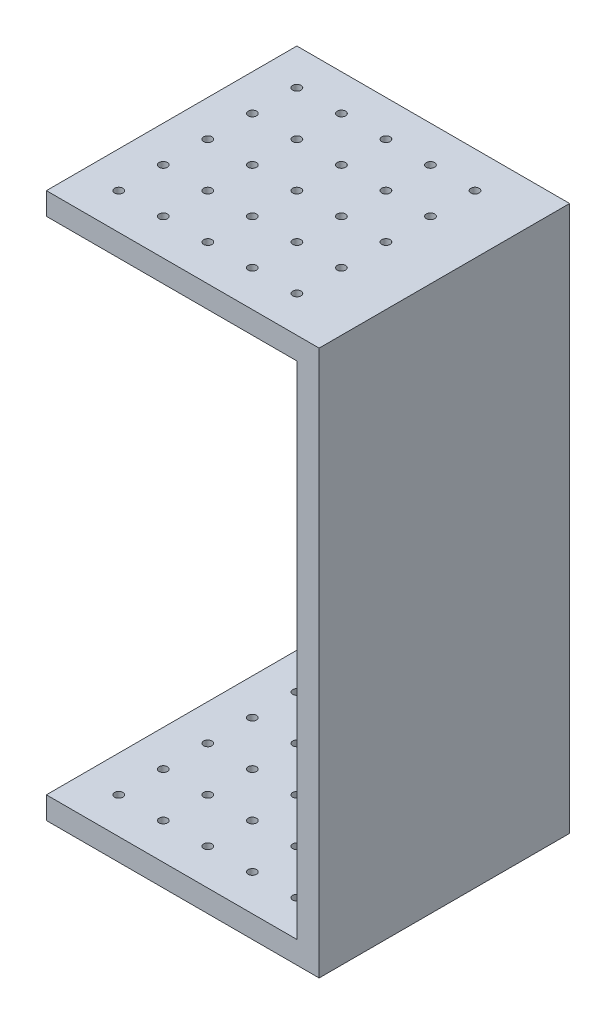
SolidWorks part; units mm, degrees
ref_plane "Front Plane" through (0, 0, 0) normal (0, 0, 1) x (1, 0, 0)
ref_plane "Top Plane" through (0, 0, 0) normal (0, 1, 0) x (1, 0, 0)
ref_plane "Right Plane" through (0, 0, 0) normal (1, 0, 0) x (0, 0, -1)
sketch "Sketch1" plane through (0, 0, 0) normal (0, 1, 0) x (1, 0, 0)
  line L1 (12.25, -11.25) -> (-12.25, -11.25)
  line L2 (12.25, -11.25) -> (12.25, 11.25)
  line L3 (12.25, 11.25) -> (-12.25, 11.25)
  line L4 (-12.25, -11.25) -> (-12.25, 11.25)
  line L5 (12.25, -11.25) -> (-12.25, 11.25) construction
  line L6 (12.25, 11.25) -> (-12.25, -11.25) construction
  point P0 (0, 0)
  dimension "D1" = 24.5
  dimension "D2" = 22.5
extrude "Boss-Extrude1" add sketch "Sketch1" along normal blind 2
sketch "Sketch2" plane through (0, 2, 0) normal (0, 1, 0) x (1, 0, 0)
  line L0 (-12.25, 11.25) -> (12.25, -11.25) construction
  line L1 (12.25, 11.25) -> (-12.25, -11.25) construction
  line L3 (12.25, 11.25) -> (-12.25, 11.25) construction
  line L5 (12.25, -11.25) -> (10.25, -11.25)
  line L7 (10.25, -11.25) -> (10.25, 11.25)
  line L8 (10.25, 11.25) -> (12.25, 11.25)
  line L9 (-12.25, -11.25) -> (12.25, -11.25) construction
  line L12 (12.25, 11.25) -> (12.25, -11.25)
  dimension "D2" = 2
extrude "Boss-Extrude2" add sketch "Sketch2" along normal blind 45
sketch "Sketch3" plane through (0, 0, 0) normal (0, -1, 0) x (1, 0, 0)
  line L0 (-9, 8) -> (-9, 11.25) construction
  line L1 (12.25, 11.25) -> (-12.25, -11.25) construction
  line L2 (-12.25, -11.25) -> (-12.25, 11.25) construction
  line L7 (-12.25, 11.25) -> (12.25, 11.25) construction
  circle A0 centre (-9, 8) radius 0.375
  dimension "D1" = 0.75
  dimension "D3" = 3.25
  dimension "D4" = 3.25
sketch "Sketch4" plane through (0, 47, 0) normal (0, 1, 0) x (1, 0, 0)
  line L1 (-12.25, 11.25) -> (12.25, 11.25)
  line L2 (-12.25, 11.25) -> (-12.25, -11.25)
  line L3 (-12.25, -11.25) -> (12.25, -11.25)
  line L4 (12.25, 11.25) -> (12.25, -11.25)
  line L5 (-12.25, 11.25) -> (12.25, -11.25) construction
  line L6 (-12.25, -11.25) -> (12.25, 11.25) construction
  point P0 (0, 0)
  dimension "D1" = 24.5
  dimension "D2" = 22.5
extrude "Boss-Extrude3" add sketch "Sketch4" along normal blind 2
extrude "Cut-Extrude1" cut sketch "Sketch3" against normal through all
pattern_linear "LPattern1" count 5 spacing 4 along (0, 0, -1) count 5 spacing 4 along (1, 0, 0) of "Cut-Extrude1"
equation "\"D1@Sketch1\"=\"D2@Sketch1\"+2"
equation "\"D4@Sketch3\"=\"D3@Sketch3\""
equation "\"D1@Sketch4\"=\"D2@Sketch4\"+2"
